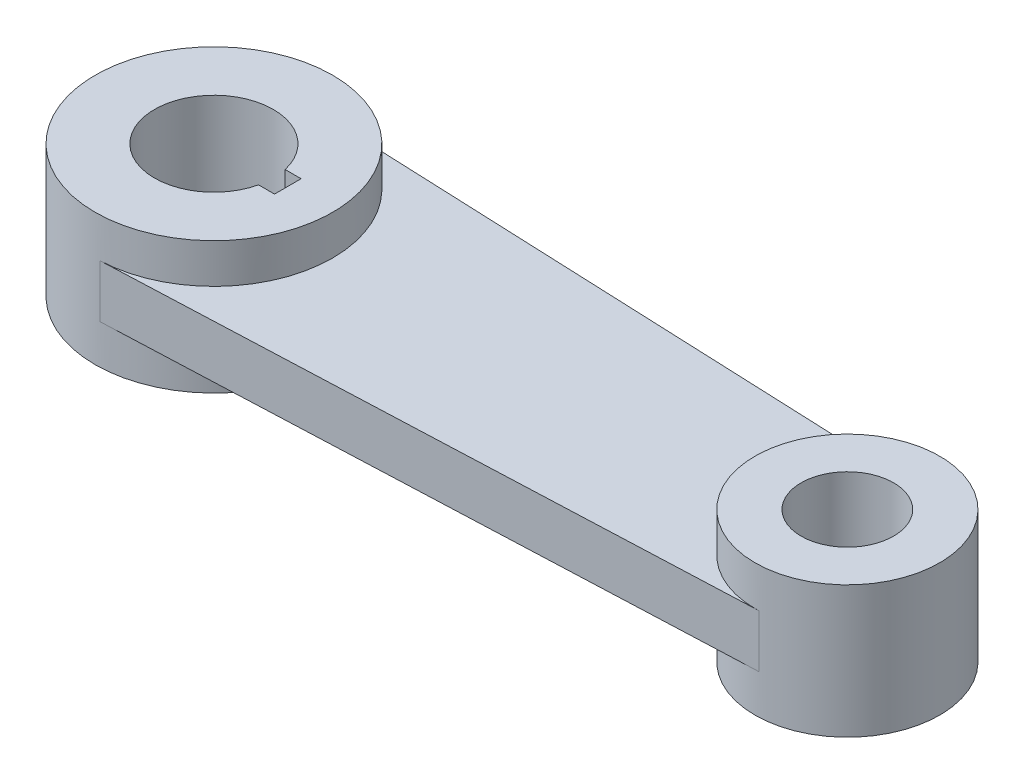
SolidWorks part; units mm, degrees
material "1060 Alloy"
ref_plane "Front Plane" through (0, 0, 0) normal (0, 0, 1) x (1, 0, 0)
ref_plane "Top Plane" through (0, 0, 0) normal (0, 1, 0) x (1, 0, 0)
ref_plane "Right Plane" through (0, 0, 0) normal (1, 0, 0) x (0, 0, -1)
sketch "Sketch1" plane through (0, 0, 0) normal (0, 1, 0) x (1, 0, 0)
  line L0 (-97.5641, 0) -> (491.8966, 0) construction
  line L1 (2.3437, 56.2012) -> (301.8229, 43.712)
  line L2 (2.3438, -56.2012) -> (301.8229, -43.712)
  line L4 (27.436, 6.3) -> (35, 6.3)
  line L6 (27.436, -6.3) -> (35, -6.3)
  line L7 (35, 6.3) -> (35, -6.3)
  arc A0 (2.3437, 56.2012) -> (2.3438, -56.2012) centre (0, 0) ccw
  arc A1 (27.436, 6.3) -> (27.436, -6.3) centre (0, 0) ccw
  arc A2 (301.8229, -43.712) -> (301.8229, 43.712) centre (300, 0) ccw
  circle A3 centre (300, 0) radius 21.9
  dimension "D1" = 87.5
  dimension "D2" = 43.8
  dimension "D3" = 112.5
  dimension "D4" = 28.15
  dimension "D5" = 300
  dimension "D6" = 12.6
  dimension "D7" = 35
extrude "Boss-Extrude1" add sketch "Sketch1" along normal mid plane 62.5
sketch "Sketch2" plane through (0, 31.25, 0) normal (0, 1, 0) x (1, 0, 0)
  line L0 (2.3438, 56.2012) -> (301.8229, 43.712)
  line L1 (2.3438, -56.2012) -> (301.8229, -43.712)
  arc A0 (2.3438, -56.2012) -> (2.3438, 56.2012) centre (0, 0) ccw
  arc A1 (301.8229, 43.712) -> (301.8229, -43.712) centre (300, 0) ccw
  dimension "D1" = 87.5
  dimension "D2" = 112.5
extrude "Cut-Extrude1" cut sketch "Sketch2" against normal blind 18.75
mirror "Mirror1" about plane through (0, 0, 0) normal (0, 1, 0) of "Cut-Extrude1"
